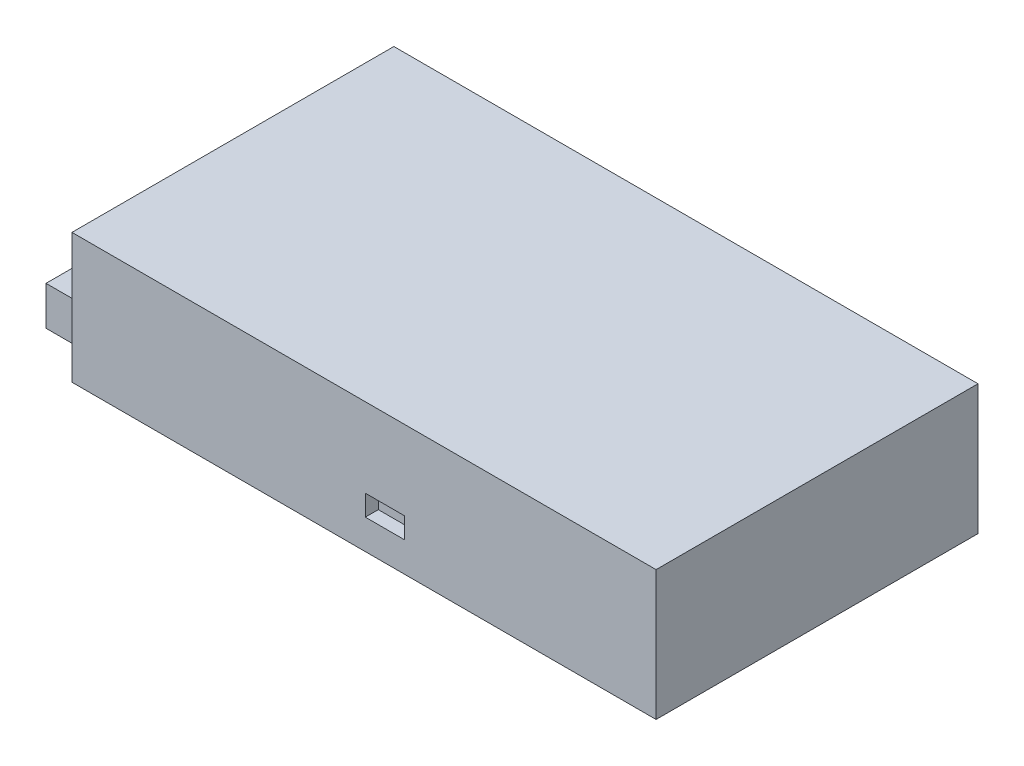
SolidWorks part; units mm, degrees
ref_plane "Front Plane" through (0, 0, 0) normal (0, 0, 1) x (1, 0, 0)
ref_plane "Top Plane" through (0, 0, 0) normal (0, 1, 0) x (1, 0, 0)
ref_plane "Right Plane" through (0, 0, 0) normal (1, 0, 0) x (0, 0, -1)
sketch "Sketch1" plane through (0, 0, 0) normal (0, 1, 0) x (1, 0, 0)
  line L0 (-112.5, 62) -> (112.5, -62) construction
  line L1 (-112.5, 62) -> (112.5, 62)
  line L2 (-112.5, 62) -> (-112.5, -62)
  line L3 (-112.5, -62) -> (112.5, -62)
  line L4 (112.5, 62) -> (112.5, -62)
  dimension "D1" = 124
  dimension "D2" = 225
extrude "Boss-Extrude1" add sketch "Sketch1" along normal blind 50
sketch "Sketch3" plane through (0, 0, 0) normal (0, -1, 0) x (1, 0, 0)
  line L0 (-112.5, 62) -> (112.5, 62) construction
  circle A0 centre (-79, -25.5) radius 2
  circle A1 centre (-79, 24.5) radius 2
  circle A2 centre (71, -25.5) radius 2
  circle A3 centre (71, 24.5) radius 2
  dimension "D5" = 4
  dimension "D1" = 37.5
  dimension "D2" = 50
  dimension "D3" = 150
  dimension "D4" = 33.5
extrude "Cut-Extrude2" cut sketch "Sketch3" against normal blind 5
sketch "Sketch4" plane through (0, 0, 62) normal (0, 0, 1) x (1, 0, 0)
  line L0 (-112.5, 0) -> (112.5, 0) construction
  line L1 (0.5, 19.5) -> (15.5, 19.5)
  line L2 (0.5, 19.5) -> (0.5, 11.5)
  line L3 (0.5, 11.5) -> (15.5, 11.5)
  line L4 (15.5, 19.5) -> (15.5, 11.5)
  line L5 (112.5, 50) -> (112.5, 0) construction
  dimension "D1" = 11.5
  dimension "D2" = 97
  dimension "D3" = 15
  dimension "D4" = 8
extrude "Cut-Extrude3" cut sketch "Sketch4" against normal blind 5
sketch "Sketch5" plane through (-112.5, 0, 0) normal (-1, 0, 0) x (0, 0, 1)
  line L0 (-62, 0) -> (62, 0) construction
  line L1 (-47, 25) -> (59, 25)
  line L2 (-47, 25) -> (-47, 10)
  line L3 (-47, 10) -> (59, 10)
  line L4 (59, 25) -> (59, 10)
  line L5 (62, 50) -> (62, 0) construction
  line L7 (-62, 50) -> (-62, 0) construction
  dimension "D1" = 10
  dimension "D2" = 3
  dimension "D3" = 15
  dimension "D4" = 15
extrude "Boss-Extrude2" add sketch "Sketch5" along normal blind 13
